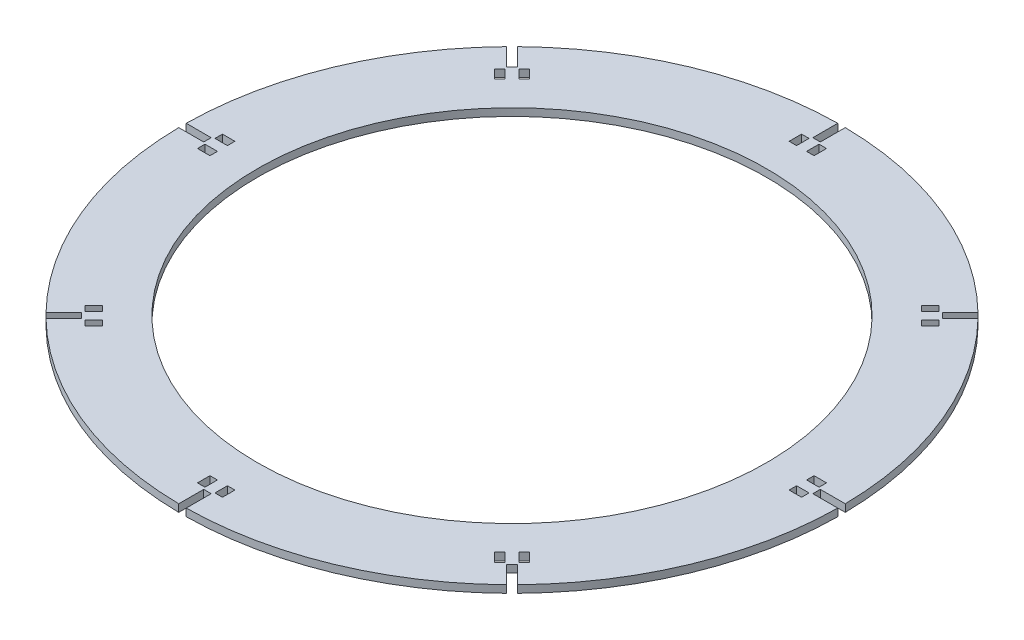
SolidWorks part; units mm, degrees
ref_plane "Front Plane" through (0, 0, 0) normal (0, 0, 1) x (1, 0, 0)
ref_plane "Top Plane" through (0, 0, 0) normal (0, 1, 0) x (1, 0, 0)
ref_plane "Right Plane" through (0, 0, 0) normal (1, 0, 0) x (0, 0, -1)
sketch "Sketch1" plane through (0, 0, 0) normal (0, 1, 0) x (1, 0, 0)
  circle A0 centre (0, 0) radius 132.01
  dimension "D1" = 264.02
extrude "Boss-Extrude1" add sketch "Sketch1" along normal blind 3
sketch "Sketch2" plane through (0, 3, 0) normal (0, 1, 0) x (1, 0, 0)
  line L0 (-1.5, 132.0015) -> (-1.5, 122.0015)
  line L1 (-1.5, 122.0015) -> (1.5, 122.0015)
  line L2 (1.5, 122.0015) -> (1.5, 132.0015)
  line L16 (0, 122.0015) -> (0, 132.01) construction
  circle A0 centre (0, 0) radius 132.01 construction
  dimension "D1" = 10
  dimension "D2" = 10
  dimension "D3" = 3
extrude "Cut-Extrude1" cut sketch "Sketch2" against normal blind 3 and the other way through all
sketch "Sketch3" plane through (0, 3, 0) normal (0, 1, 0) x (1, 0, 0)
  line L0 (0, 0) -> (0, 43.9961) construction
pattern_circular "CirPattern1" count 8 over 360 about axis through (0, 3, 0) along (0, 0, -1) of "Cut-Extrude1"
sketch "Sketch7" plane through (0, 3, 0) normal (0, 1, 0) x (1, 0, 0)
  line L0 (-5, 121.0015) -> (-2, 121.0015)
  line L1 (-5, 121.0015) -> (-5, 116.0015)
  line L2 (-5, 116.0015) -> (-2, 116.0015)
  line L3 (-2, 121.0015) -> (-2, 116.0015)
  line L4 (0, 122.0015) -> (0, 116.8402) construction
  line L5 (2, 121.0015) -> (2, 116.0015)
  line L6 (5, 116.0015) -> (2, 116.0015)
  line L7 (5, 121.0015) -> (5, 116.0015)
  line L8 (5, 121.0015) -> (2, 121.0015)
  line L9 (-1.5, 122.0015) -> (1.5, 122.0015) construction
  line L10 (-1.5, 132.0015) -> (-1.5, 122.0015) construction
  dimension "D1" = 3
  dimension "D2" = 5
  dimension "D3" = 0.5
  dimension "D4" = 1
extrude "Cut-Extrude4" cut sketch "Sketch7" against normal blind 3
pattern_circular "CirPattern2" count 8 over 360 about axis through (0, 0, 0) along (0, 1, 0) of "Cut-Extrude4"
sketch "Sketch8" plane through (0, 3, 0) normal (0, 1, 0) x (1, 0, 0)
  circle A0 centre (0, 0) radius 102.01
  dimension "D1" = 204.02
extrude "Cut-Extrude6" cut sketch "Sketch8" against normal blind 10
sketch "Sketch9" plane through (0, 3, 0) normal (0, 1, 0) x (1, 0, 0)
  text T0 "B5" font "Century Gothic" height in points 22
  dimension "D1" = 105
  dimension "D2" = 4
